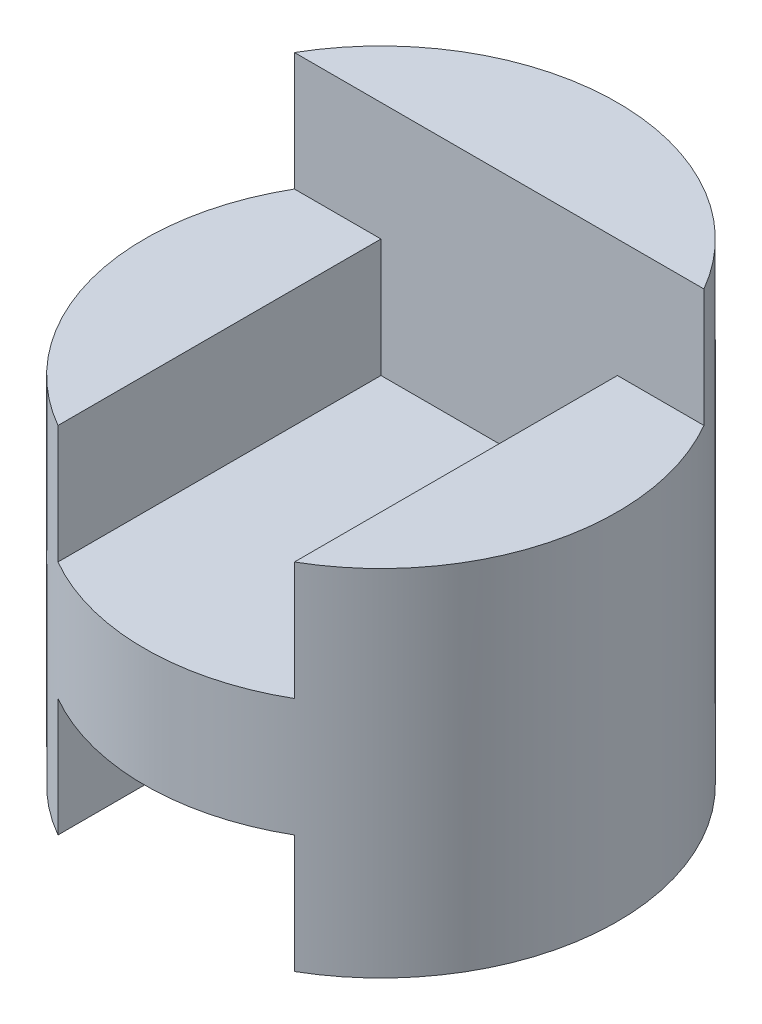
SolidWorks part; units mm, degrees
ref_plane "Front" through (0, 0, 0) normal (0, 0, 1) x (1, 0, 0)
ref_plane "Top" through (0, 0, 0) normal (0, 1, 0) x (1, 0, 0)
ref_plane "Right" through (0, 0, 0) normal (1, 0, 0) x (0, 0, -1)
sketch "Sketch1" plane through (0, 0, 0) normal (0, 1, 0) x (1, 0, 0)
  circle A0 centre (0, 0) radius 2
  dimension "D1" = 4
extrude "Boss-Extrude1" add sketch "Sketch1" along normal blind 4
sketch "Sketch2" plane through (0, 0, 0) normal (0, 0, 1) x (1, 0, 0)
  line L0 (-2, 4) -> (2, 4)
  line L1 (2, 4) -> (2, 3)
  line L2 (2, 0) -> (2, 4) construction
  line L3 (2, 3) -> (1, 3)
  line L4 (1, 3) -> (1, 2)
  line L5 (1, 2) -> (-1, 2)
  line L6 (-1, 2) -> (-1, 3)
  line L7 (-1, 3) -> (-2, 3)
  line L8 (-2, 3) -> (-2, 4)
  line L9 (-2, 0) -> (2, 0) construction
  line L10 (-1, 0) -> (1, 0)
  line L11 (-1, 0) -> (-1, 1)
  line L12 (-1, 1) -> (1, 1)
  line L13 (1, 0) -> (1, 1)
  dimension "D1" = 1
  dimension "D2" = 1
  dimension "D3" = 1
  dimension "D4" = 1
  dimension "D5" = 1
  dimension "D6" = 1
extrude "Cut-Extrude1" cut sketch "Sketch2" against normal blind 1 and the other way blind 3
